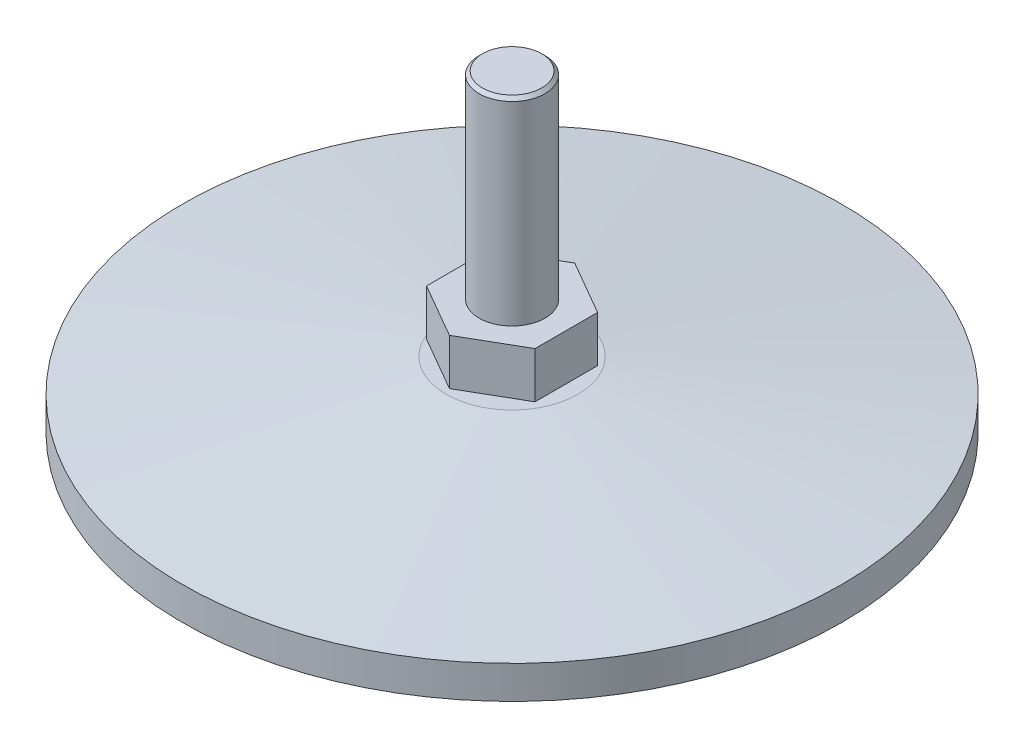
SolidWorks part; units mm, degrees
ref_plane "Спереди" through (0, 0, 0) normal (0, 0, 1) x (1, 0, 0)
ref_plane "Сверху" through (0, 0, 0) normal (0, 1, 0) x (1, 0, 0)
ref_plane "Справа" through (0, 0, 0) normal (1, 0, 0) x (0, 0, -1)
sketch "Эскиз1" plane through (0, 0, 0) normal (0, 0, 1) x (1, 0, 0)
  line L0 (0, 0) -> (0, 47.5) construction
  line L1 (0, 47.5) -> (-5, 47.5)
  line L2 (-5, 47.5) -> (-5, 17.5)
  line L3 (-5, 17.5) -> (-9.5, 17.5)
  line L4 (-9.5, 17.5) -> (-9.5, 10.5)
  line L5 (-9.5, 10.5) -> (-5, 10.5)
  line L6 (-5, 10.5) -> (-5, 10)
  line L7 (-5, 10) -> (-10, 10)
  line L8 (-10, 10) -> (-50, 5)
  line L9 (-50, 5) -> (-50, 0)
  line L10 (-50, 0) -> (-5, 0)
  line L11 (0, 7) -> (0, 47.5)
  line L12 (0, 7) -> (-5, 7)
  line L13 (-5, 7) -> (-5, 0)
  line L14 (-5, 0) -> (0, 0) construction
  dimension "D1" = 50
  dimension "D2" = 5
  dimension "D3" = 10
  dimension "D4" = 10
  dimension "D5" = 9.5
  dimension "D6" = 0.5
  dimension "D7" = 7
  dimension "D8" = 5
  dimension "D9" = 5
  dimension "D10" = 30
  dimension "D11" = 5
  dimension "D12" = 7
revolve "Повернуть1" add sketch "Эскиз1" angle 360 about L0
cosmetic thread "Условное изображение резьбы1" parameters "D2"=8.344
chamfer "Фаска1" distance 0.5 angle 45 1 edges at (5, 47.5, 0)
sketch "Эскиз2" plane through (0, 17.5, 0) normal (0, 1, 0) x (1, 0, 0)
  line L1 (0, 9.5) -> (-8.2272, 4.75)
  line L2 (-8.2272, 4.75) -> (-8.2272, -4.75)
  line L3 (-8.2272, -4.75) -> (0, -9.5)
  line L4 (0, -9.5) -> (8.2272, -4.75)
  line L5 (8.2272, -4.75) -> (8.2272, 4.75)
  line L6 (8.2272, 4.75) -> (0, 9.5)
  circle A0 centre (0, 0) radius 12.1398
  circle A1 centre (0, 0) radius 8.2272 construction
  circle A2 centre (0, 0) radius 9.5 construction
extrude "Вырез-Вытянуть1" cut sketch "Эскиз2" against normal up to next
